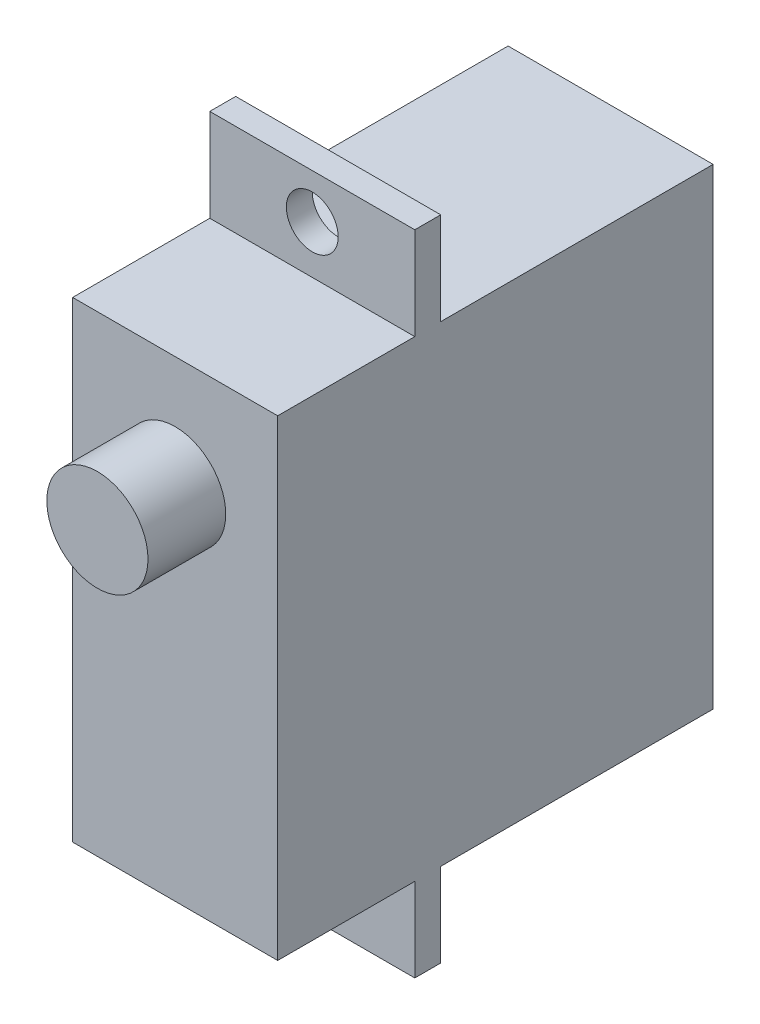
SolidWorks part; units mm, degrees
ref_plane "前视基准面" through (0, 0, 0) normal (0, 0, 1) x (1, 0, 0)
ref_plane "上视基准面" through (0, 0, 0) normal (0, 1, 0) x (1, 0, 0)
ref_plane "右视基准面" through (0, 0, 0) normal (1, 0, 0) x (0, 0, -1)
sketch "Sketch1" plane through (0, 0, 0) normal (1, 0, 0) x (0, 0, -1)
  line L1 (-14.76, 15.6242) -> (2.04, 15.6242)
  line L2 (-14.76, 15.6242) -> (-14.76, -2.5758)
  line L3 (-14.76, -2.5758) -> (2.04, -2.5758)
  line L4 (2.04, 15.6242) -> (2.04, -2.5758)
  line L5 (-14.76, 15.6242) -> (2.04, -2.5758) construction
  line L6 (-14.76, -2.5758) -> (2.04, 15.6242) construction
  point P0 (-6.36, 6.5242)
  dimension "D1" = 16.8
  dimension "D2" = 18.2
extrude "Boss-Extrude1" add sketch "Sketch1" along normal blind 7.91
sketch "Sketch2" plane through (7.91, 0, 0) normal (1, 0, 0) x (0, 0, -1)
  line L0 (2.04, -2.5758) -> (2.04, 15.6242) construction
  line L1 (-9.47, 19.1945) -> (-8.47, 19.1945)
  line L2 (-9.47, 19.1945) -> (-9.47, -5.8055)
  line L3 (-9.47, -5.8055) -> (-8.47, -5.8055)
  line L4 (-8.47, 19.1945) -> (-8.47, -5.8055)
  dimension "D1" = 10.51
  dimension "D2" = 1
  dimension "D3" = 25
extrude "Boss-Extrude2" add sketch "Sketch2" against normal up to surface (7.91 mm away) contours L1 L4 L3 L2 up to face at (0, 6.5242, 6.36)
sketch "Sketch3" plane through (0, 0, 9.47) normal (0, 0, 1) x (1, 0, 0)
  line L0 (0, 15.6242) -> (0, -2.5758) construction
  line L1 (-3.955, -4.4308) -> (3.955, -4.4308) construction
  line L2 (-3.955, -4.4308) -> (-3.955, 17.4792) construction
  line L3 (-3.955, 17.4792) -> (3.955, 17.4792) construction
  line L4 (3.955, -4.4308) -> (3.955, 17.4792) construction
  line L5 (-3.955, -4.4308) -> (3.955, 17.4792) construction
  line L6 (-3.955, 17.4792) -> (3.955, -4.4308) construction
  circle A0 centre (3.955, 17.4792) radius 1
  circle A1 centre (3.955, -4.4308) radius 1
  point P0 (0, 6.5242)
  point P10 (3.955, -4.2073)
  dimension "D1" = 21.91
extrude "Cut-Extrude1" cut sketch "Sketch3" against normal blind 21.9
sketch "Sketch4" plane through (0, 0, 14.76) normal (0, 0, 1) x (1, 0, 0)
  circle A0 centre (3.955, 11.3332) radius 1.9516
extrude "Boss-Extrude3" add sketch "Sketch4" along normal blind 3
equation "\"16。8\"=83.7992"
